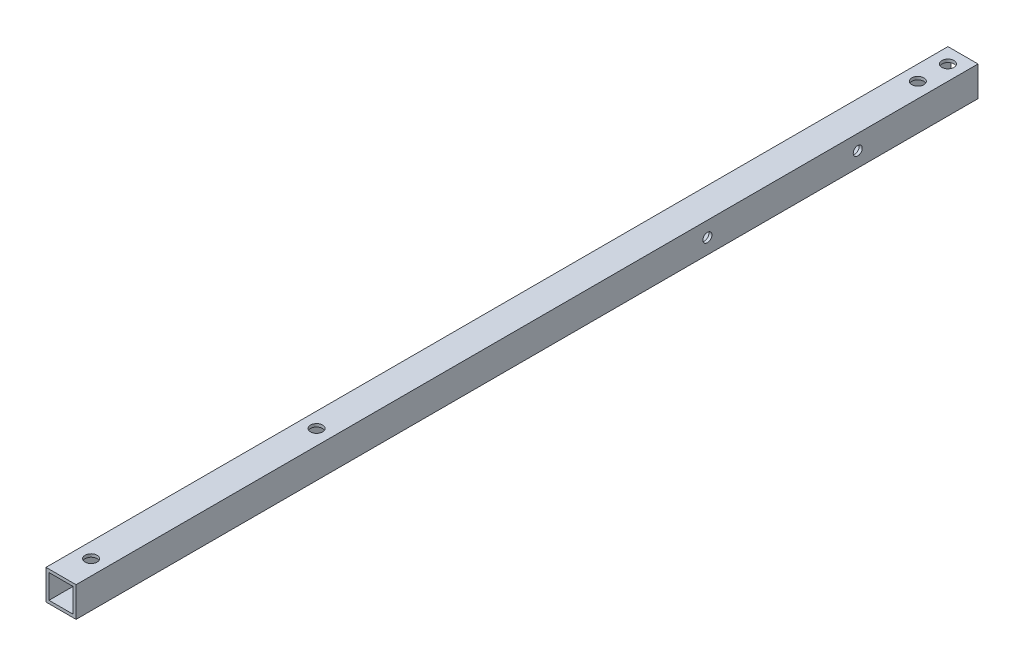
SolidWorks part; units mm, degrees
material "1060 Сплав"
ref_plane "Спереди" through (0, 0, 0) normal (0, 0, 1) x (1, 0, 0)
ref_plane "Сверху" through (0, 0, 0) normal (0, 1, 0) x (1, 0, 0)
ref_plane "Справа" through (0, 0, 0) normal (1, 0, 0) x (0, 0, -1)
sketch "Эскиз1" plane through (0, 0, 0) normal (0, 0, 1) x (1, 0, 0)
  line L0 (1, -1) -> (9, -1)
  line L1 (0, 0) -> (10, 0)
  line L2 (0, 0) -> (0, -10)
  line L3 (0, -10) -> (10, -10)
  line L4 (10, 0) -> (10, -10)
  line L5 (9, -1) -> (9, -9)
  line L6 (1, -9) -> (9, -9)
  line L7 (1, -1) -> (1, -9)
  dimension "D1" = 10
  dimension "D2" = 1
extrude "Бобышка-Вытянуть1" add sketch "Эскиз1" along normal blind 300
sketch "Эскиз2" plane through (0, 0, 0) normal (0, 1, 0) x (1, 0, 0)
  line L0 (5, 0) -> (5, -300) construction
  line L1 (10, 0) -> (0, 0) construction
  line L2 (10, -300) -> (0, -300) construction
  line L3 (0, -300) -> (10, -300) construction
  circle A0 centre (5, -5) radius 2
  circle A1 centre (5, -15) radius 2
  circle A2 centre (5, -290) radius 2
  circle A3 centre (5, -215) radius 2
  dimension "D1" = 4
  dimension "D2" = 4
  dimension "D4" = 5
  dimension "D3" = 10
  dimension "D5" = 10
  dimension "D6" = 75
extrude "Вырез-Вытянуть1" cut sketch "Эскиз2" against normal through all
sketch "Эскиз3" plane through (10, 0, 0) normal (1, 0, 0) x (0, 0, -1)
  line L0 (0, -5) -> (-300, -5) construction
  line L1 (0, -10) -> (0, 0) construction
  line L2 (-300, -10) -> (-300, 0) construction
  circle A0 centre (-40, -5) radius 1.5
  circle A1 centre (-90, -5) radius 1.5
  dimension "D1" = 3
  dimension "D2" = 50
  dimension "D3" = 40
extrude "Вырез-Вытянуть2" cut sketch "Эскиз3" against normal through all
